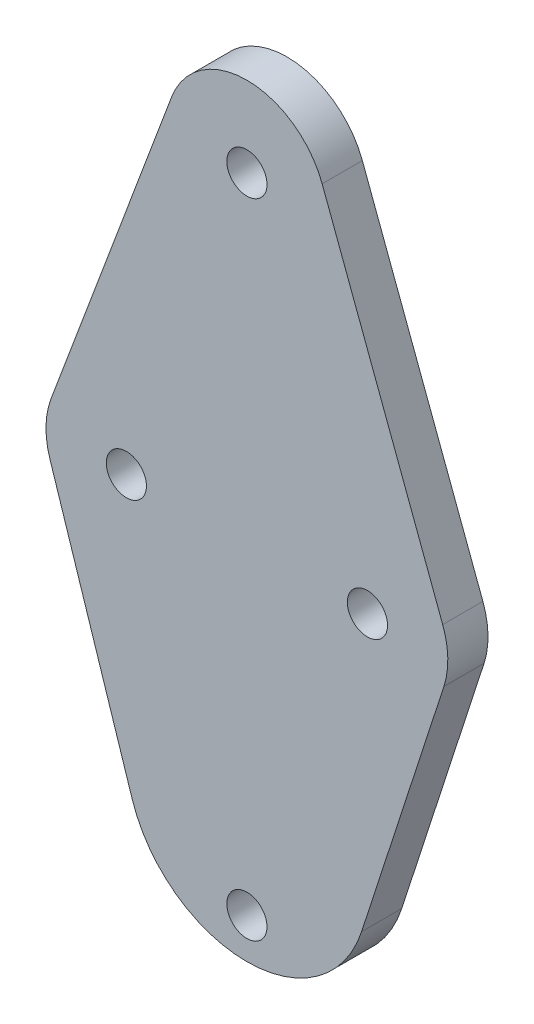
SolidWorks part; units mm, degrees
ref_plane "Front Plane" through (0, 0, 0) normal (0, 0, 1) x (1, 0, 0)
ref_plane "Top Plane" through (0, 0, 0) normal (0, 1, 0) x (1, 0, 0)
ref_plane "Right Plane" through (0, 0, 0) normal (1, 0, 0) x (0, 0, -1)
sketch "Sketch1" plane through (0, 0, 0) normal (0, 0, 1) x (1, 0, 0)
  line L0 (24.3633, 3.5112) -> (9.3633, 43.5112)
  line L1 (-9.3633, 43.5112) -> (-24.3633, 3.5112)
  line L2 (-24.511, -3.0888) -> (-14.2665, -34.6332)
  line L3 (14.2665, -34.6332) -> (24.511, -3.0888)
  arc A0 (9.3633, 43.5112) -> (-9.3633, 43.5112) centre (0, 40) ccw
  arc A1 (-14.2665, -34.6332) -> (14.2665, -34.6332) centre (0, -30) ccw
  arc A2 (24.3633, 3.5112) -> (24.511, -3.0888) centre (15, 0) cw
  arc A3 (-24.3633, 3.5112) -> (-24.511, -3.0888) centre (-15, 0) ccw
  dimension "D1" = 10
  dimension "D2" = 10
  dimension "D3" = 15
  dimension "D4" = 70
  dimension "D5" = 30
  dimension "D6" = 40
extrude "Boss-Extrude1" add sketch "Sketch1" along normal blind 5
sketch "Sketch2" plane through (0, 0, 5) normal (0, 0, 1) x (1, 0, 0)
  line L0 (-15, 0) -> (15, 0) construction
  circle A0 centre (0, 40) radius 2.5
  circle A1 centre (0, -40) radius 2.5
  circle A2 centre (15, 0) radius 2.5
  circle A3 centre (-15, 0) radius 2.5
  point P8 (0, 0)
  dimension "D1" = 5
  dimension "D2" = 30
  dimension "D4" = 80
  dimension "D5" = 40
extrude "Cut-Extrude1" cut sketch "Sketch2" against normal through all
